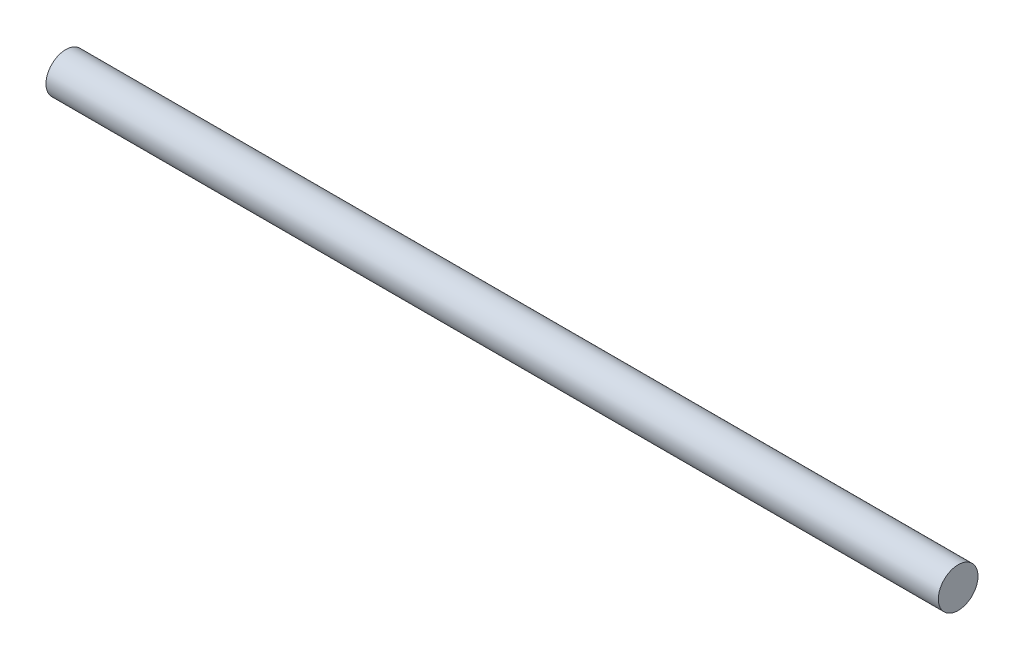
SolidWorks part; units mm, degrees
material "Stainless Steel (ferritic)"
ref_plane "Front Plane" through (0, 0, 0) normal (0, 0, 1) x (1, 0, 0)
ref_plane "Top Plane" through (0, 0, 0) normal (0, 1, 0) x (1, 0, 0)
ref_plane "Right Plane" through (0, 0, 0) normal (1, 0, 0) x (0, 0, -1)
sketch "Sketch1" plane through (0, 0, 0) normal (1, 0, 0) x (0, 0, -1)
  circle A0 centre (0, 0) radius 10
  dimension "D1" = 20
extrude "Boss-Extrude1" add sketch "Sketch1" along normal blind 450 contours A0
